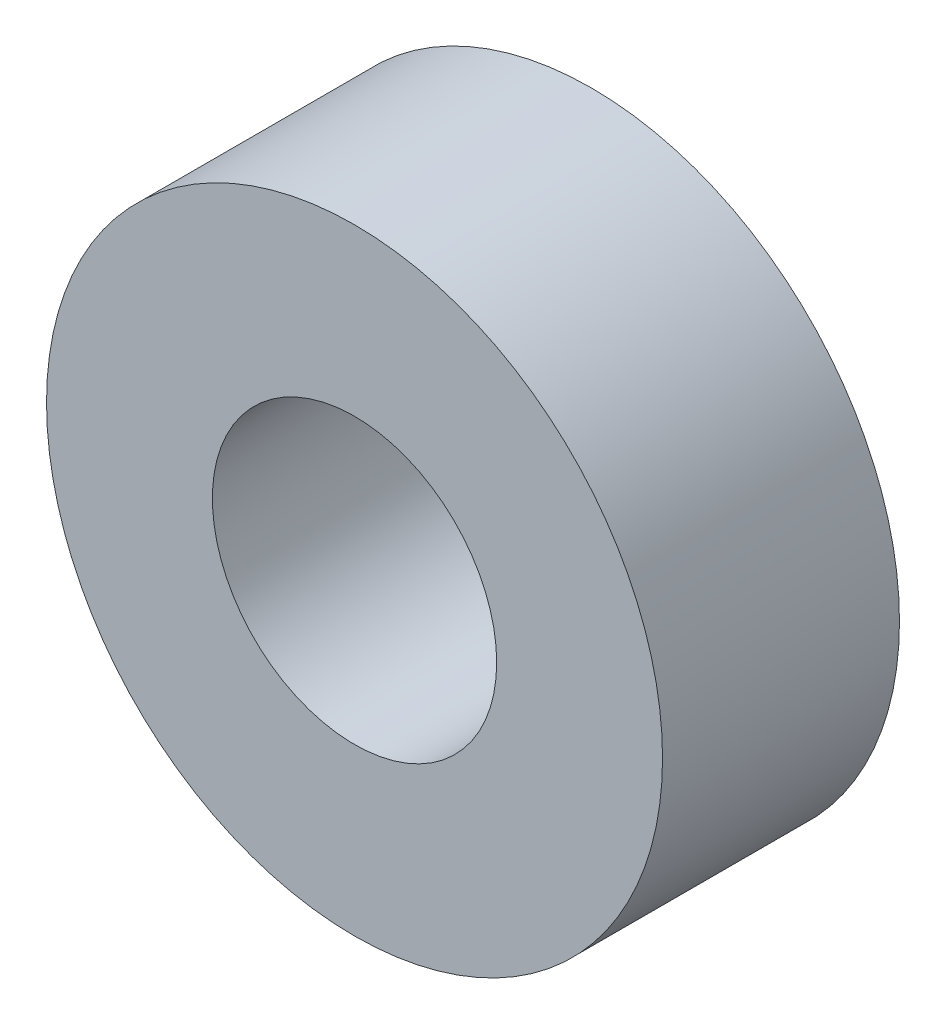
SolidWorks part; units mm, degrees
material "1060 合金"
ref_plane "前视基准面" through (0, 0, 0) normal (0, 0, 1) x (1, 0, 0)
ref_plane "上视基准面" through (0, 0, 0) normal (0, 1, 0) x (1, 0, 0)
ref_plane "右视基准面" through (0, 0, 0) normal (1, 0, 0) x (0, 0, -1)
other "Configuration Table"
sketch "草图1" plane through (0, 0, 0) normal (0, 0, 1) x (1, 0, 0)
  circle A0 centre (0, 0) radius 3
  circle A1 centre (0, 0) radius 6.5
  dimension "D1" = 6
  dimension "D2" = 13
extrude "凸台-拉伸1" add sketch "草图1" along normal mid plane 5
